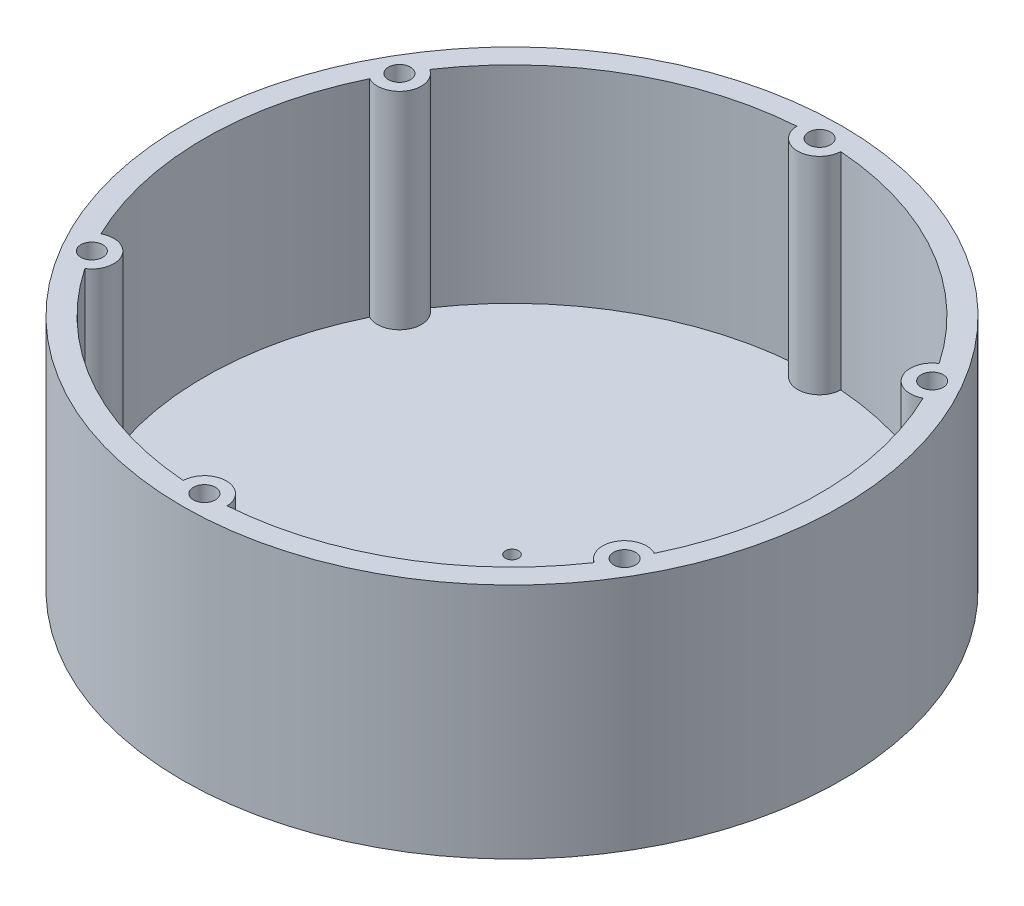
SolidWorks part; units mm, degrees
ref_plane "Front Plane" through (0, 0, 0) normal (0, 0, 1) x (1, 0, 0)
ref_plane "Top Plane" through (0, 0, 0) normal (0, 1, 0) x (1, 0, 0)
ref_plane "Right Plane" through (0, 0, 0) normal (1, 0, 0) x (0, 0, -1)
sketch "Sketch1" plane through (0, 0, 0) normal (0, 1, 0) x (1, 0, 0)
  circle A0 centre (0, 0) radius 75
  dimension "D1" = 150
extrude "Boss-Extrude1" add sketch "Sketch1" along normal blind 5
sketch "Sketch2" plane through (0, 5, 0) normal (0, 1, 0) x (1, 0, 0)
  circle A0 centre (0, 0) radius 65
  circle A2 centre (0, 0) radius 75
  circle A3 centre (0, 0) radius 75
  dimension "D1" = 10
  dimension "D2" = 0
extrude "Boss-Extrude2" add sketch "Sketch2" along normal blind 47
sketch "Sketch3" plane through (0, 52, 0) normal (0, 1, 0) x (1, 0, 0)
  circle A0 centre (0, 0) radius 70 construction
  circle A1 centre (0, 70) radius 2.5
  circle A2 centre (60.6218, 35) radius 2.5
  circle A3 centre (60.6218, -35) radius 2.5
  circle A4 centre (0, -70) radius 2.5
  circle A5 centre (-60.6218, -35) radius 2.5
  circle A6 centre (-60.6218, 35) radius 2.5
  dimension "D1" = 140
  dimension "D2" = 5
  dimension "D3" = 6
extrude "Cut-Extrude1" cut sketch "Sketch3" against normal blind 16
sketch "Sketch4" plane through (0, 0, 0) normal (0, -1, 0) x (1, 0, 0)
  circle A0 centre (0, 0) radius 1.5
  dimension "D1" = 3
extrude "Cut-Extrude2" cut sketch "Sketch4" against normal up to next
sketch "Sketch6" plane through (0, 52, 0) normal (0, 1, 0) x (1, 0, 0)
  arc A0 (-62.9655, 30.5833) -> (-62.9655, -30.5833) centre (0, 0) ccw
  circle A1 centre (0, 0) radius 75 construction
  arc A2 (-4.9968, 69.8214) -> (4.9968, 69.8214) centre (0, 70) ccw
  circle A3 centre (0, 0) radius 75 construction
  arc A4 (57.9687, 39.2381) -> (62.9655, 30.5833) centre (60.6218, 35) ccw
  arc A5 (62.9655, -30.5833) -> (57.9687, -39.2381) centre (60.6218, -35) ccw
  arc A6 (4.9968, -69.8214) -> (-4.9968, -69.8214) centre (0, -70) ccw
  arc A7 (-57.9687, -39.2381) -> (-62.9655, -30.5833) centre (-60.6218, -35) ccw
  arc A8 (-62.9655, 30.5833) -> (-57.9687, 39.2381) centre (-60.6218, 35) ccw
  arc A9 (-57.9687, -39.2381) -> (-4.9968, -69.8214) centre (0, 0) ccw
  arc A10 (4.9968, -69.8214) -> (57.9687, -39.2381) centre (0, 0) ccw
  arc A11 (62.9655, -30.5833) -> (62.9655, 30.5833) centre (0, 0) ccw
  arc A12 (57.9687, 39.2381) -> (4.9968, 69.8214) centre (0, 0) ccw
  arc A13 (-4.9968, 69.8214) -> (-57.9687, 39.2381) centre (0, 0) ccw
  circle A14 centre (0, 0) radius 60
  point P22 (0, 0)
  dimension "D1" = 5
  dimension "D3" = 10
  dimension "D2" = 6
extrude "Cut-Extrude3" cut sketch "Sketch6" against normal up to surface (47 mm away) up to face at (0, 5, 1.5)
sketch "Sketch7" plane through (0, 0, 0) normal (0, -1, 0) x (1, 0, 0)
  circle A0 centre (0, 0) radius 75
  circle A1 centre (0, 0) radius 65
  circle A2 centre (0, 0) radius 75 construction
  dimension "D1" = 10
extrude "Boss-Extrude3" add sketch "Sketch7" along normal blind 2
sketch "Sketch8" plane through (0, -2, 0) normal (0, -1, 0) x (1, 0, 0)
  circle A0 centre (0, 0) radius 70
  circle A1 centre (0, 0) radius 75 construction
  dimension "D1" = 5
sweep "Cut-Sweep1" cut path "Sketch8" circular profile diameter 5.8 parameters "D3"=5.8
sketch "Sketch9" plane through (0, -2, 0) normal (0, -1, 0) x (1, 0, 0)
  circle A0 centre (0, 0) radius 70
  circle A1 centre (0, 0) radius 72.9 construction
  circle A2 centre (0, 0) radius 67.1 construction
  dimension "D1" = 5.8
  dimension "D2" = 2.9
